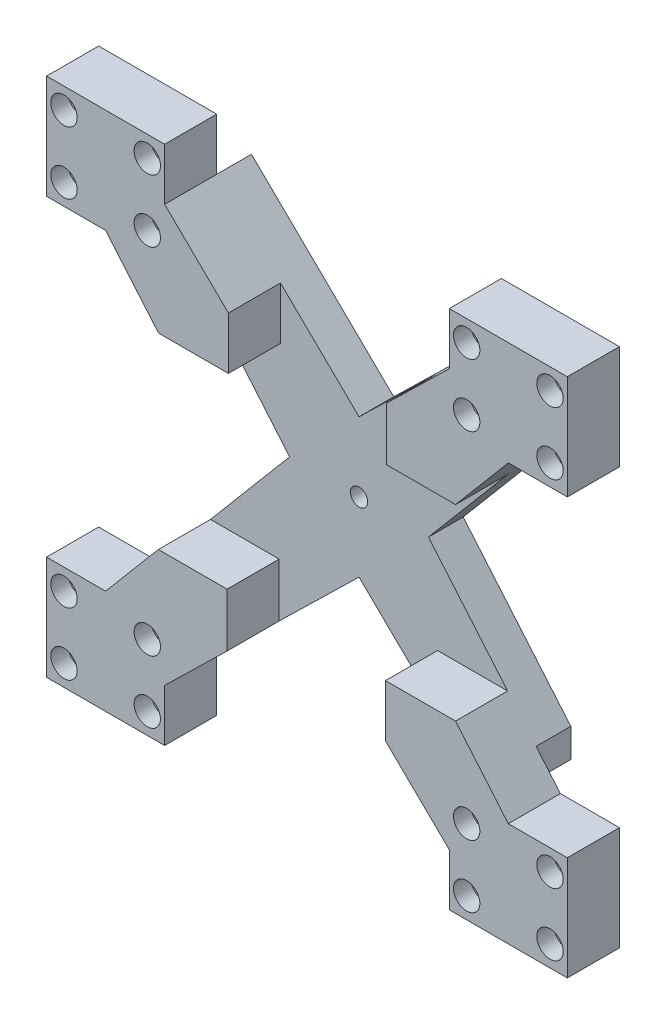
SolidWorks part; units mm, degrees
ref_plane "Front Plane" through (0, 0, 0) normal (0, 0, 1) x (1, 0, 0)
ref_plane "Top Plane" through (0, 0, 0) normal (0, 1, 0) x (1, 0, 0)
ref_plane "Right Plane" through (0, 0, 0) normal (1, 0, 0) x (0, 0, -1)
sketch "Sketch1" plane through (0, 0, 0) normal (0, 0, 1) x (1, 0, 0)
  line L1 (-75, -75) -> (75, -75)
  line L2 (-75, -75) -> (-75, 75)
  line L3 (-75, 75) -> (75, 75)
  line L4 (75, -75) -> (75, 75)
  line L5 (-75, -75) -> (75, 75) construction
  line L6 (-75, 75) -> (75, -75) construction
  point P0 (0, 0)
  dimension "D1" = 150
  dimension "D2" = 150
extrude "Boss-Extrude1" add sketch "Sketch1" along normal blind 15
sketch "Sketch2" plane through (0, 0, 15) normal (0, 0, 1) x (1, 0, 0)
  line L0 (-41, 60) -> (0, 20)
  line L1 (-75, 75) -> (-41, 75)
  line L2 (-75, 75) -> (-75, 45)
  line L3 (-75, 45) -> (-41, 45)
  line L4 (-41, 75) -> (-41, 45)
  line L5 (75, 75) -> (41, 75)
  line L6 (75, 75) -> (75, 45)
  line L7 (75, 45) -> (41, 45)
  line L8 (41, 75) -> (41, 45)
  line L9 (-75, -75) -> (-41, -75)
  line L10 (-75, -75) -> (-75, -45)
  line L11 (-75, -45) -> (-41, -45)
  line L12 (-41, -75) -> (-41, -45)
  line L13 (75, -75) -> (41, -75)
  line L14 (75, -75) -> (75, -45)
  line L15 (75, -45) -> (41, -45)
  line L16 (41, -75) -> (41, -45)
  line L17 (-20, -20) -> (20, -20)
  line L18 (-20, -20) -> (-20, 20)
  line L19 (-20, 20) -> (20, 20)
  line L20 (20, -20) -> (20, 20)
  line L21 (-20, -20) -> (20, 20) construction
  line L22 (-20, 20) -> (20, -20) construction
  line L23 (0, 20) -> (41, 60)
  line L24 (-58, -45) -> (-20, 0)
  line L25 (-20, 0) -> (-58, 45)
  line L26 (-41, -60) -> (0, -20)
  line L27 (0, -20) -> (41, -60)
  line L28 (58, 45) -> (20, 0)
  line L29 (20, 0) -> (58, -45)
  point P20 (0, 0)
  line M15 (75, -75) -> (75, 75)
  line M16 (75, 75) -> (-75, 75)
  line M17 (-75, 75) -> (-75, -75)
  line M18 (-75, -75) -> (75, -75)
  dimension "D1" = 34
  dimension "D2" = 30
  dimension "D3" = 34
  dimension "D4" = 30
  dimension "D5" = 30
  dimension "D6" = 30
  dimension "D7" = 34
  dimension "D8" = 34
  dimension "D9" = 40
  dimension "D10" = 40
extrude "Cut-Extrude1" cut sketch "Sketch2" against normal blind 15 contours L0 L23 L8 L4 M16 | L24 L25 L3 L11 M17 | L28 L29 L15 L7 M15 | L27 L26 L12 L16 M18
sketch "Sketch3" plane through (0, 0, 15) normal (0, 0, 1) x (1, 0, 0)
  line L0 (-58, 45.0694) -> (-20, 0)
  line L1 (-41, -75) -> (-75, -75)
  line L2 (-41, -75) -> (-41, -45)
  line L3 (-41, -45) -> (-75, -45)
  line L4 (-75, -75) -> (-75, -45)
  line L5 (-75, 75) -> (-41, 75)
  line L6 (-75, 75) -> (-75, 45.0694)
  line L7 (-75, 45.0694) -> (-41, 45.0694)
  line L8 (-41, 75) -> (-41, 45.0694)
  line L9 (75, 45) -> (41, 45)
  line L10 (75, 45) -> (75, 75)
  line L11 (75, 75) -> (41, 75)
  line L12 (41, 45) -> (41, 75)
  line L13 (41, -75) -> (75, -75)
  line L14 (41, -75) -> (41, -45)
  line L15 (41, -45) -> (75, -45)
  line L16 (75, -75) -> (75, -45)
  line L17 (-20, 0) -> (-58, -45)
  line L18 (-41, 60.0347) -> (0, 20)
  line L19 (0, 20) -> (41, 60)
  line L20 (58, 45) -> (20, 0)
  line L21 (20, 0) -> (58, -45)
  line L22 (41, -60) -> (0, -20)
  line L23 (0, -20) -> (-41, -60)
  line M9 (-20, 0) -> (-58, -45)
  line M14 (-41, -60) -> (0, -20)
  line M15 (0, -20) -> (41, -60)
  line M20 (58, -45) -> (20, 0)
  line M21 (20, 0) -> (58, 45)
  line M26 (41, 60) -> (0, 20)
  line M27 (0, 20) -> (-41, 60)
extrude "Boss-Extrude2" add sketch "Sketch3" against normal blind 25 contours L14 L15 L9 L12 L8 L7 L0 L3 L2 M20 M21 M26 M27 M9 M14 M15
sketch "Sketch4" plane through (0, 0, 15) normal (0, 0, 1) x (1, 0, 0)
  line L0 (-38, -57.0732) -> (-41, -60)
  line L1 (-75, 45) -> (-41, 45)
  line L2 (-75, 45) -> (-75, 75)
  line L3 (-75, 75) -> (-41, 75)
  line L4 (-41, 45) -> (-41, 75)
  line L5 (75, 45) -> (41, 45)
  line L6 (75, 45) -> (75, 75)
  line L7 (75, 75) -> (41, 75)
  line L8 (41, 45) -> (41, 75)
  line L9 (41, -75) -> (75, -75)
  line L10 (41, -75) -> (41, -45)
  line L11 (41, -45) -> (75, -45)
  line L12 (75, -75) -> (75, -45)
  line L13 (-41, -75) -> (-75, -75)
  line L14 (-41, -75) -> (-41, -45)
  line L15 (-41, -45) -> (-75, -45)
  line L16 (-75, -75) -> (-75, -45)
  line L17 (0, 20) -> (-37.2207, 56.3128)
  line L18 (-41, 60) -> (0, 20) construction
  line L19 (41, -60) -> (38, -57.0732)
  line L20 (-58, 45) -> (-55.4667, 42)
  line L21 (0, -20) -> (41, -60) construction
  line L22 (0, 20) -> (-37.4263, 56.5134)
  line L23 (38, -57.0732) -> (38, -42)
  line L24 (-58, -45) -> (-55.4667, -42)
  line L25 (-58, -45) -> (-20, 0) construction
  line L26 (-55.4667, -42) -> (-38, -42)
  line L27 (-38, -42) -> (-38, -57.0732)
  line L28 (-41, -60) -> (0, -20) construction
  line L29 (38, -42) -> (55.4667, -42)
  line L30 (20, 0) -> (58, -45) construction
  line L31 (55.4667, -42) -> (58, -45)
  line L32 (-20, 0) -> (-58, 45) construction
  line L33 (-55.4667, 42) -> (-38, 42)
  line L34 (-38, 42) -> (-38, 57.0732)
  line L35 (-38, 57.0732) -> (-41, 60)
  line L36 (41, 60) -> (37.925, 57)
  line L37 (0, 20) -> (41, 60) construction
  line L38 (37.925, 57) -> (37.925, 42)
  line L39 (37.925, 42) -> (55.4667, 42)
  line L40 (58, 45) -> (20, 0) construction
  line L41 (55.4667, 42) -> (58, 45)
  line M9 (0, -20) -> (41, -60)
  line M14 (58, -45) -> (20, 0)
  line M15 (20, 0) -> (58, 45)
  line M20 (41, 60) -> (0, 20)
  line M21 (0, 20) -> (-41, 60)
  line M26 (-58, 45) -> (-20, 0)
  line M27 (-20, 0) -> (-58, -45)
  line M32 (-41, -60) -> (0, -20)
  dimension "D1" = 3
  dimension "D2" = 3
  dimension "D3" = 3
  dimension "D4" = 3
  dimension "D5" = 3
  dimension "D6" = 3
  dimension "D7" = 3
  dimension "D8" = 3
extrude "Cut-Extrude2" cut sketch "Sketch4" against normal blind 15 contours L39 L38 L34 L33 L26 L27 L23 L29 M20 M21 M26 M27 M32 M9 M14 M15 | L6 L5 L8 L7
sketch "Sketch5" plane through (0, 0, 0) normal (0, 0, 1) x (1, 0, 0)
  circle A0 centre (0, 0) radius 2.5
  dimension "D1" = 5
extrude "Cut-Extrude3" cut sketch "Sketch5" against normal blind 15
sketch "Sketch7" plane through (0, 0, 15) normal (0, 0, 1) x (1, 0, 0)
  line L0 (75, -45) -> (58, -45) construction
  line L1 (75, -75) -> (75, -45) construction
  line L2 (41, -75) -> (75, -75) construction
  line L3 (41, -75) -> (41, -60) construction
  circle A0 centre (70, -51) radius 2.5
  circle A1 centre (46, -51) radius 2.5
  circle A2 centre (46, -69) radius 2.5
  circle A3 centre (70, -69) radius 2.5
  dimension "D1" = 5
  dimension "D2" = 5
  dimension "D3" = 5
  dimension "D4" = 5
  dimension "D5" = 6
  dimension "D6" = 5
  dimension "D7" = 5
  dimension "D8" = 6
  dimension "D9" = 5
  dimension "D10" = 6
  dimension "D11" = 6
  dimension "D12" = 5
extrude "Cut-Extrude4" cut sketch "Sketch7" against normal blind 15
sketch "Sketch8" plane through (0, 0, 15) normal (0, 0, 1) x (1, 0, 0)
  circle A0 centre (46, -51) radius 3.8
  circle A1 centre (70, -51) radius 3.8
  circle A2 centre (70, -69) radius 3.8
  circle A3 centre (46, -69) radius 3.8
  dimension "D1" = 7.6
  dimension "D2" = 7.6
  dimension "D3" = 7.6
  dimension "D4" = 7.6
extrude "Cut-Extrude5" cut sketch "Sketch8" against normal blind 5
sketch "Sketch10" plane through (0, 0, 15) normal (0, 0, 1) x (1, 0, 0)
  line L0 (-75, -75) -> (-41, -75) construction
  line L1 (-75, -45) -> (-75, -75) construction
  line L2 (-41, -75) -> (-41, -60) construction
  line L3 (-75, -45) -> (-58, -45) construction
  circle A0 centre (-46, -69) radius 2.5
  circle A1 centre (-46, -51) radius 2.5
  circle A2 centre (-70, -51) radius 2.5
  circle A3 centre (-70, -69) radius 2.5
  dimension "D1" = 5
  dimension "D2" = 5
  dimension "D3" = 5
  dimension "D4" = 5
  dimension "D5" = 6
  dimension "D6" = 5
  dimension "D7" = 6
  dimension "D8" = 5
  dimension "D10" = 5
  dimension "D11" = 5
  dimension "D12" = 6
  dimension "D9" = 6
extrude "Cut-Extrude6" cut sketch "Sketch10" against normal through all
sketch "Sketch11" plane through (0, 0, 15) normal (0, 0, 1) x (1, 0, 0)
  circle A0 centre (-70, -51) radius 3.8
  circle A1 centre (-46, -51) radius 3.8
  circle A2 centre (-70, -69) radius 3.8
  circle A3 centre (-46, -69) radius 3.8
  dimension "D1" = 7.6
  dimension "D2" = 7.6
  dimension "D3" = 7.6
  dimension "D4" = 7.6
extrude "Cut-Extrude7" cut sketch "Sketch11" against normal blind 5
sketch "Sketch12" plane through (0, 0, 15) normal (0, 0, 1) x (1, 0, 0)
  line L0 (75, 75) -> (41, 75) construction
  line L1 (75, 45) -> (75, 75) construction
  line L2 (75, 45) -> (58, 45) construction
  line L3 (41, 75) -> (41, 60) construction
  circle A0 centre (46, 69) radius 2.5
  circle A1 centre (70, 69) radius 2.5
  circle A2 centre (70, 51) radius 2.5
  circle A3 centre (46, 51) radius 2.5
  dimension "D1" = 5
  dimension "D2" = 5
  dimension "D3" = 5
  dimension "D4" = 5
  dimension "D5" = 6
  dimension "D6" = 5
  dimension "D7" = 6
  dimension "D8" = 5
  dimension "D9" = 6
  dimension "D10" = 5
  dimension "D11" = 6
  dimension "D12" = 5
extrude "Cut-Extrude8" cut sketch "Sketch12" against normal through all
sketch "Sketch13" plane through (0, 0, 15) normal (0, 0, 1) x (1, 0, 0)
  circle A0 centre (70, 69) radius 3.8
  circle A1 centre (46, 69) radius 3.8
  circle A2 centre (46, 51) radius 3.8
  circle A3 centre (70, 51) radius 3.8
  dimension "D1" = 7.6
  dimension "D2" = 7.6
  dimension "D3" = 7.6
  dimension "D4" = 7.6
extrude "Cut-Extrude9" cut sketch "Sketch13" against normal blind 5
sketch "Sketch14" plane through (0, 0, 15) normal (0, 0, 1) x (1, 0, 0)
  line L0 (-75, 45) -> (-58, 45) construction
  line L1 (-41, 75) -> (-41, 60) construction
  line L2 (-41, 75) -> (-75, 75) construction
  line L3 (-75, 75) -> (-75, 45) construction
  circle A0 centre (-70, 69) radius 2.5
  circle A1 centre (-46, 69) radius 2.5
  circle A2 centre (-46, 51) radius 2.5
  circle A3 centre (-70, 51) radius 2.5
  dimension "D1" = 5
  dimension "D2" = 5
  dimension "D3" = 5
  dimension "D4" = 5
  dimension "D5" = 6
  dimension "D6" = 6
  dimension "D7" = 5
  dimension "D8" = 5
  dimension "D10" = 6
  dimension "D11" = 5
  dimension "D12" = 5
  dimension "D9" = 6
extrude "Cut-Extrude10" cut sketch "Sketch14" against normal through all
sketch "Sketch15" plane through (0, 0, 15) normal (0, 0, 1) x (1, 0, 0)
  circle A0 centre (-70, 69) radius 3.8
  circle A1 centre (-46, 69) radius 3.8
  circle A2 centre (-46, 51) radius 3.8
  circle A3 centre (-70, 51) radius 3.8
  dimension "D1" = 7.6
  dimension "D2" = 7.6
  dimension "D3" = 7.6
  dimension "D4" = 7.6
extrude "Cut-Extrude11" cut sketch "Sketch15" against normal blind 5
sketch "Sketch16" plane through (0, 0, 0) normal (0, 0, 1) x (1, 0, 0)
  line L0 (-38, -57.0732) -> (-23, -42.439)
  line L1 (-38, -57.0732) -> (0, -20) construction
  line L2 (-23, -42.439) -> (-23, -27)
  line L3 (-23, -27) -> (-42.8, -27)
  line L4 (-20, 0) -> (-55.4667, -42) construction
  line L5 (-42.8, -27) -> (-55.4667, -42)
  line L6 (-55.4667, -42) -> (-38, -42) construction
  line L7 (-55.4667, -42) -> (-38, -42) construction
  line L8 (-55.4667, -42) -> (-38, -42)
  line L9 (-38, -42) -> (-38, -57.0732) construction
  line L10 (-38, -42) -> (-38, -57.0732)
  dimension "D1" = 15
  dimension "D2" = 15
extrude "Boss-Extrude3" add sketch "Sketch16" along normal blind 15
sketch "Sketch17" plane through (0, 0, 0) normal (0, 0, 1) x (1, 0, 0)
  line L0 (38, -57.0732) -> (22.625, -42.0732)
  line L1 (0, -20) -> (38, -57.0732) construction
  line L2 (22.625, -42.0732) -> (22.625, -27)
  line L3 (22.625, -27) -> (42.8, -27)
  line L4 (55.4667, -42) -> (20, 0) construction
  line L5 (42.8, -27) -> (55.4667, -42)
  line L6 (55.4667, -42) -> (38, -42)
  line L7 (38, -42) -> (38, -57.0732)
  dimension "D1" = 15
  dimension "D2" = 15
extrude "Boss-Extrude4" add sketch "Sketch17" along normal blind 15
sketch "Sketch18" plane through (0, 0, 0) normal (0, 0, 1) x (1, 0, 0)
  line L0 (37.925, 57) -> (22.925, 42.3659)
  line L1 (37.925, 57) -> (0, 20) construction
  line L2 (22.925, 42.3659) -> (22.925, 27)
  line L3 (22.925, 27) -> (42.8, 27)
  line L4 (20, 0) -> (55.4667, 42) construction
  line L5 (42.8, 27) -> (55.4667, 42)
  line L6 (55.4667, 42) -> (37.925, 42)
  line L7 (37.925, 42) -> (37.925, 57)
  dimension "D1" = 15
  dimension "D2" = 15
extrude "Boss-Extrude5" add sketch "Sketch18" along normal blind 15
sketch "Sketch19" plane through (0, 0, 0) normal (0, 0, 1) x (1, 0, 0)
  line L0 (-38, 57.0732) -> (-22.625, 42.0732)
  line L1 (0, 20) -> (-38, 57.0732) construction
  line L2 (-22.625, 42.0732) -> (-22.625, 27)
  line L3 (-22.625, 27) -> (-42.7649, 27)
  line L4 (-20, 0) -> (-55.412, 42) construction
  line L5 (-42.7649, 27) -> (-55.4667, 42)
  line L6 (-55.4667, 42) -> (-38, 42)
  line L7 (-38, 42) -> (-38, 57.0732)
  dimension "D1" = 15
  dimension "D2" = 15
extrude "Boss-Extrude6" add sketch "Sketch19" along normal blind 15
sketch "Sketch20" plane through (0, -75, 0) normal (0, -1, 0) x (1, 0, 0)
  line L0 (41, -10) -> (58, -10) construction
  line L1 (58, 0) -> (51, 0)
  line L2 (58, 0) -> (58, -10)
  line L3 (58, -10) -> (51, -10)
  line L4 (51, 0) -> (51, -10)
  dimension "D1" = 7
extrude "Cut-Extrude12" cut sketch "Sketch20" against normal through all
sketch "Sketch21" plane through (0, -45, 0) normal (0, -1, 0) x (1, 0, 0)
  line L0 (-75, 0) -> (-41, 0) construction
  line L1 (-58, 0) -> (-51, 0)
  line L2 (-58, 0) -> (-58, -10)
  line L3 (-58, -10) -> (-51, -10)
  line L4 (-51, 0) -> (-51, -10)
  line L5 (-41, -10) -> (-58, -10) construction
  dimension "D1" = 7
extrude "Cut-Extrude13" cut sketch "Sketch21" against normal through all
